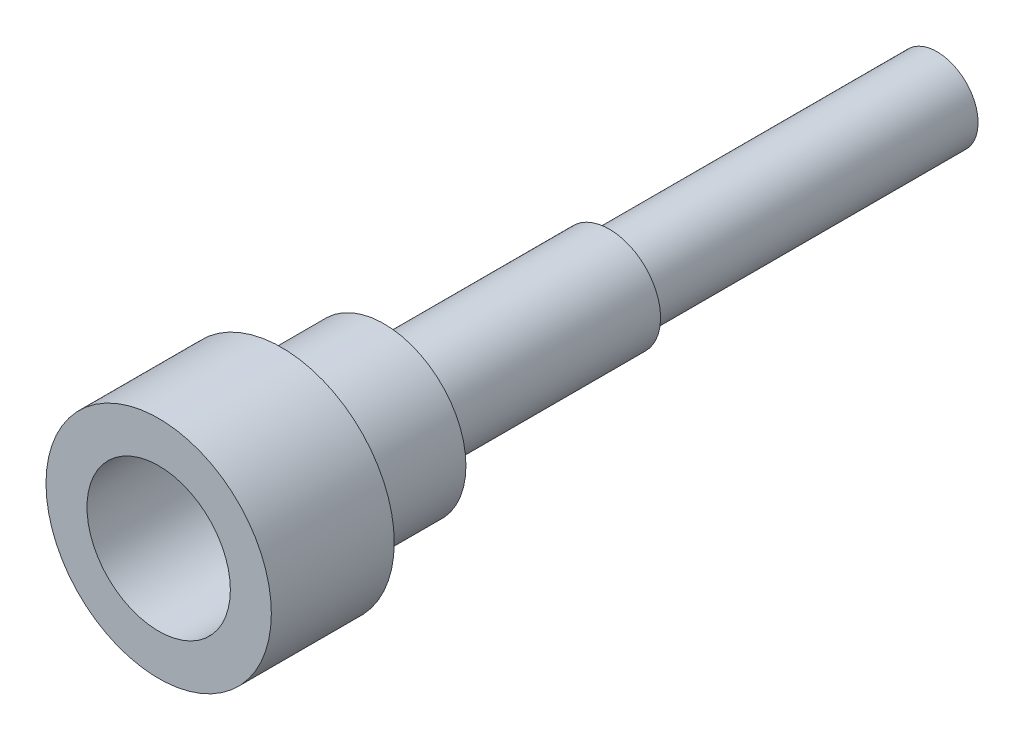
SolidWorks part; units mm, degrees
ref_plane "Alzado" through (0, 0, 0) normal (0, 0, 1) x (1, 0, 0)
ref_plane "Planta" through (0, 0, 0) normal (0, 1, 0) x (1, 0, 0)
ref_plane "Vista lateral" through (0, 0, 0) normal (1, 0, 0) x (0, 0, -1)
sketch "Croquis1" plane through (0, 0, 0) normal (0, 0, 1) x (1, 0, 0)
  circle A0 centre (0, 0) radius 4
  dimension "D1" = 8
extrude "Saliente-Extruir1" add sketch "Croquis1" along normal blind 5
sketch "Croquis2" plane through (0, 0, 5) normal (0, 0, 1) x (1, 0, 0)
  circle A0 centre (0, 0) radius 5.5
  circle A1 centre (0, 0) radius 3.5
  dimension "D1" = 11
  dimension "D2" = 7
extrude "Saliente-Extruir2" add sketch "Croquis2" along normal blind 6
sketch "Croquis3" plane through (0, 0, 0) normal (0, 0, -1) x (-1, 0, 0)
  circle A0 centre (0, 0) radius 2.5
  dimension "D1" = 5
extrude "Saliente-Extruir3" add sketch "Croquis3" along normal blind 11
sketch "Croquis4" plane through (0, 0, -11) normal (0, 0, -1) x (-1, 0, 0)
  circle A0 centre (0, 0) radius 2
  dimension "D1" = 4
extrude "Saliente-Extruir4" add sketch "Croquis4" along normal blind 16
sketch "Croquis5" plane through (0, 0, 0) normal (0, 1, 0) x (1, 0, 0)
  line L0 (2.5, 11) -> (-2.5, 11) construction
  circle A0 centre (0, 9.5) radius 0.75
  dimension "D1" = 1.5
  dimension "D2" = 1.5
extrude "Cortar-Extruir1" cut sketch "Croquis5" against normal through all
